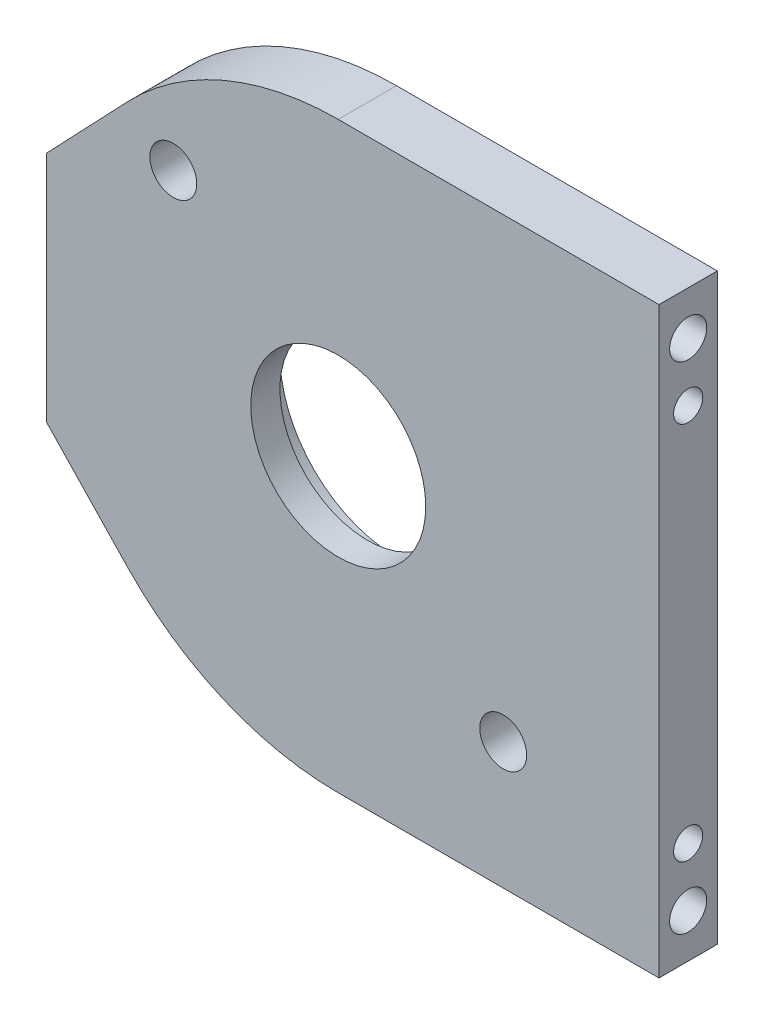
SolidWorks part; units mm, degrees
material "6061-T6 (SS)"
ref_plane "Front Plane" through (0, 0, 0) normal (0, 0, 1) x (1, 0, 0)
ref_plane "Top Plane" through (0, 0, 0) normal (0, 1, 0) x (1, 0, 0)
ref_plane "Right Plane" through (0, 0, 0) normal (1, 0, 0) x (0, 0, -1)
sketch "Sketch1" plane through (0, 0, 0) normal (0, 0, 1) x (1, 0, 0)
  line L0 (34.925, 31.75) -> (34.925, -31.75)
  line L1 (34.925, 0) -> (24.0681, 0) construction
  line L2 (34.925, 31.75) -> (0, 31.75)
  line L3 (34.925, -31.75) -> (0, -31.75)
  line L4 (-31.75, 12.7) -> (-31.75, -12.7)
  line L5 (-22.9914, 21.8966) -> (-31.75, 12.7)
  line L6 (-22.9914, -21.8966) -> (-31.75, -12.7)
  line L7 (-31.75, 0) -> (0, 0) construction
  arc A0 (-22.9914, -21.8966) -> (0, -31.75) centre (0, 0) ccw
  circle A1 centre (0, 0) radius 9.525
  arc A2 (0, 31.75) -> (-22.9914, 21.8966) centre (0, 0) ccw
  dimension "D1" = 63.5
  dimension "D2" = 19.05
  dimension "D3" = 3.175
  dimension "D4" = 63.5
  dimension "D5" = 31.75
  dimension "D7" = 25.4
extrude "Boss-Extrude1" add sketch "Sketch1" along normal blind 6.35
hole_wizard "#10 Clearance Hole1" positions "Sketch2" profile "Sketch3" hole size "#10" standard "ANSI Inch" end condition through all
sketch "Sketch2" plane through (0, 0, 6.35) normal (0, 0, 1) x (1, 0, 0)
  line L0 (-17.9605, 17.9605) -> (17.9605, -17.9605) construction
  line L2 (-1000, 0) -> (49000, 0) construction
  circle A0 centre (0, 0) radius 25.4
  point P5 (-17.9605, 17.9605)
  point P7 (17.9605, -17.9605)
  dimension "D1" = 50.8
  dimension "D2" = 45
sketch "Sketch3" plane through (17.9605, -17.9605, 6.35) normal (1, 0, 0) x (0, -1, 0)
  line L0 (0, 0) -> (0, 6.35)
  line L1 (0, 6.35) -> (2.5527, 6.35)
  line L2 (2.5527, 6.35) -> (2.5527, 0)
  line L5 (2.5527, 0) -> (0, 0)
  line L11 (0, -6.35) -> (0, 107.95) construction
  dimension "Thru Hole Dia." = 5.1054
  dimension "Thru Hole Depth" = 6.35
hole_wizard "1/8 (0.125) Transitional Dowel Hole1" positions "Sketch4" profile "Sketch5" hole size "1/8" standard "ANSI Inch"
sketch "Sketch4" plane through (34.925, 0, 0) normal (1, 0, 0) x (0, 0, -1)
  line L0 (-3.175, 20.6375) -> (-3.175, 31.75)
  line L1 (-6.35, 31.75) -> (0, 31.75) construction
  line L4 (-3.175, -20.6375) -> (-3.175, -31.75)
  line L5 (-6.35, -31.75) -> (0, -31.75) construction
  line L7 (-6.35, -31.75) -> (-6.35, 31.75) construction
  point P0 (-3.175, 20.6375)
  point P2 (-3.175, -20.6375)
  dimension "D1" = 3.175
  dimension "D2" = 41.275
sketch "Sketch5" plane through (34.925, 20.6375, 3.175) normal (0, 1, 0) x (0, 0, -1)
  line L0 (0, 0) -> (0, 11.1139)
  line L1 (0, 11.1139) -> (1.5875, 10.16)
  line L2 (1.5875, 10.16) -> (1.5875, 0)
  line L5 (1.5875, 0) -> (0, 0)
  line L10 (0, 11.1139) -> (-1.5875, 10.16) construction
  line L11 (0, -6.35) -> (0, 107.95) construction
  dimension "Hole Dia." = 3.175
  dimension "Hole Depth" = 10.16
  dimension "Drill Angle" = 118
sketch "Sketch6" plane through (0, 0, 0) normal (0, 0, 1) x (1, 0, 0)
  circle A0 centre (0, 0) radius 12.7
  dimension "D1" = 25.4
extrude "Cut-Extrude1" cut sketch "Sketch6" along normal blind 3.175
hole_wizard "#10-32 Tapped Hole1" positions "Sketch7" profile "Sketch8" tap size "#10-32" standard "ANSI Inch"
sketch "Sketch7" plane through (34.925, 0, 0) normal (1, 0, 0) x (0, 0, -1)
  line L0 (-3.175, 20.6375) -> (-3.175, 26.9875)
  line L2 (-3.175, -20.6375) -> (-3.175, -26.9875)
  point P0 (-3.175, 26.9875)
  point P2 (-3.175, -26.9875)
  dimension "D1" = 53.975
sketch "Sketch8" plane through (34.925, 26.9875, 3.175) normal (0, 1, 0) x (0, 0, -1)
  line L0 (0, 0) -> (0, 16.9613)
  line L1 (0, 16.9613) -> (2.0193, 15.748)
  line L2 (2.0193, 15.748) -> (2.0193, 0)
  line L5 (2.0193, 0) -> (0, 0)
  line L10 (0, 16.9613) -> (-2.0193, 15.748) construction
  line L11 (0, -6.35) -> (0, 107.95) construction
  dimension "Tap Drill Dia." = 4.0386
  dimension "Tap Drill Depth" = 15.748
  dimension "Drill Angle" = 118
cosmetic thread "Hole Thread1" parameters "D1"=13.462, "D2"=4.826
cosmetic thread "Hole Thread2" parameters "D1"=13.462, "D2"=4.826
hole_wizard "1/8 (0.125) Press Dowel Hole1" positions "Sketch9" profile "Sketch10" hole size "1/8" standard "ANSI Inch"
sketch "Sketch9" plane through (-31.75, 0, 0) normal (-1, 0, 0) x (0, 0, 1)
  line L1 (3.175, 7.9375) -> (3.175, 12.7) construction
  line L2 (6.35, 12.7) -> (0, 12.7) construction
  line L5 (3.175, -7.9375) -> (3.175, -12.7) construction
  line L6 (6.35, -12.7) -> (0, -12.7) construction
  point P0 (3.175, 7.9375)
  point P2 (3.175, -7.9375)
  dimension "D1" = 15.875
sketch "Sketch10" plane through (-31.75, 7.9375, 3.175) normal (0, 1, 0) x (0, 0, 1)
  line L0 (0, 0) -> (0, 7.3039)
  line L1 (0, 7.3039) -> (1.5875, 6.35)
  line L2 (1.5875, 6.35) -> (1.5875, 0)
  line L5 (1.5875, 0) -> (0, 0)
  line L10 (0, 7.3039) -> (-1.5875, 6.35) construction
  line L11 (0, -6.35) -> (0, 107.95) construction
  dimension "Hole Dia." = 3.175
  dimension "Hole Depth" = 6.35
  dimension "Drill Angle" = 118
hole_wizard "#10-32 Tapped Hole2" positions "Sketch11" profile "Sketch12" tap size "#10-32" standard "ANSI Inch"
sketch "Sketch11" plane through (-31.75, 0, 0) normal (-1, 0, 0) x (0, 0, 1)
  line L0 (3.175, 7.9375) -> (3.175, 0) construction
  line L1 (3.175, 0) -> (3.175, -7.9375) construction
  point P0 (3.175, 0)
sketch "Sketch12" plane through (-31.75, 0, 3.175) normal (0, 1, 0) x (0, 0, 1)
  line L0 (0, 0) -> (0, 16.9613)
  line L1 (0, 16.9613) -> (2.0193, 15.748)
  line L2 (2.0193, 15.748) -> (2.0193, 0)
  line L5 (2.0193, 0) -> (0, 0)
  line L10 (0, 16.9613) -> (-2.0193, 15.748) construction
  line L11 (0, -6.35) -> (0, 107.95) construction
  dimension "Tap Drill Dia." = 4.0386
  dimension "Tap Drill Depth" = 15.748
  dimension "Drill Angle" = 118
cosmetic thread "Hole Thread3" parameters "D1"=13.462, "D2"=4.826
